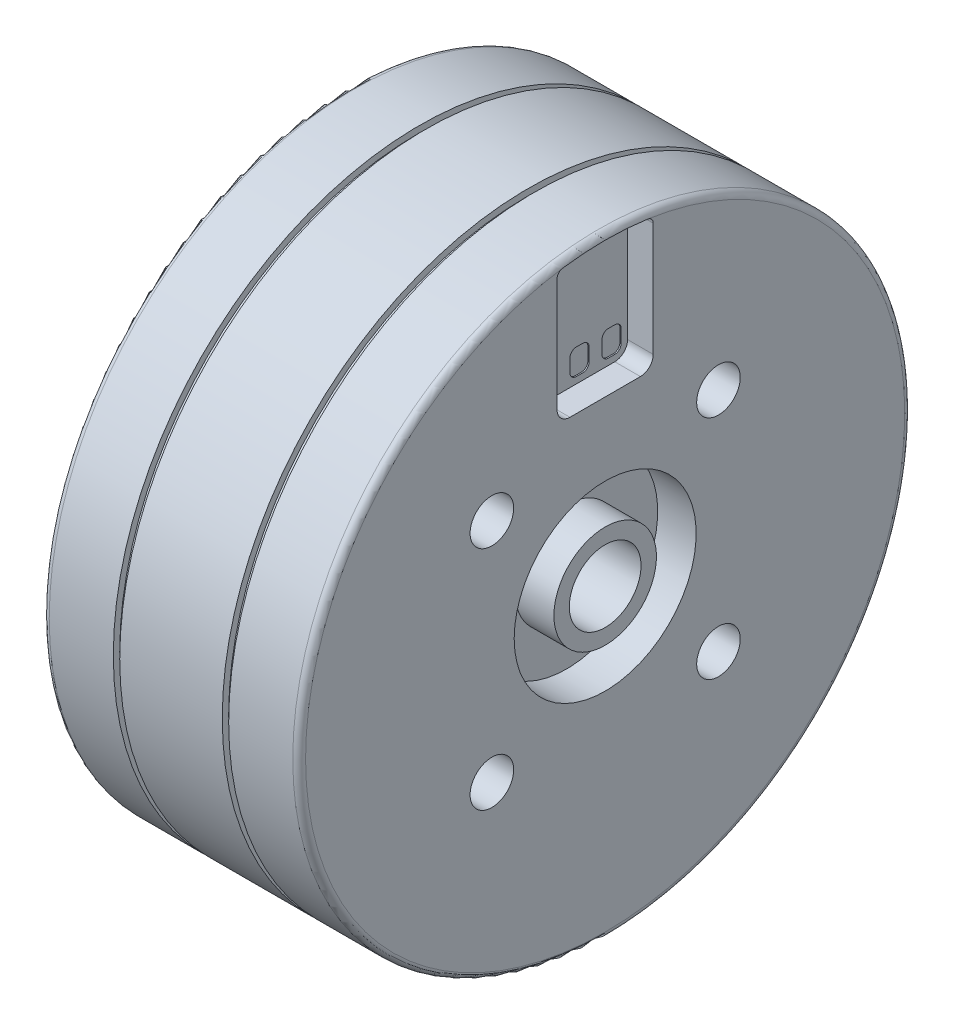
SolidWorks part; units mm, degrees
ref_plane "Plan de face" through (0, 0, 0) normal (0, 0, 1) x (1, 0, 0)
ref_plane "Plan de dessus" through (0, 0, 0) normal (0, 1, 0) x (1, 0, 0)
ref_plane "Plan de droite" through (0, 0, 0) normal (1, 0, 0) x (0, 0, -1)
sketch "Esquisse1" plane through (0, 0, 0) normal (0, 0, 1) x (1, 0, 0)
  line L0 (-88.5968, 0) -> (128.6117, 0) construction
  line L1 (0, 2.8) -> (0, 23.375)
  line L5 (6, 23.875) -> (14, 23.875)
  line L9 (20, 23.375) -> (20, 7.1)
  line L14 (20, 2.8) -> (0, 2.8)
  line L15 (0.5, 23.875) -> (5.5, 23.875)
  line L16 (14.5, 23.875) -> (19.5, 23.875)
  line L17 (5.5, 23.875) -> (5.5, 23.375)
  line L18 (5.5, 23.375) -> (6, 23.375)
  line L19 (6, 23.375) -> (6, 23.875)
  line L20 (14, 23.875) -> (14, 23.375)
  line L21 (14, 23.375) -> (14.5, 23.375)
  line L22 (14.5, 23.375) -> (14.5, 23.875)
  line L24 (17, 7.1) -> (20, 7.1)
  line L25 (20, 2.8) -> (20, 4)
  line L26 (20, 4) -> (17, 4)
  line L27 (17, 4) -> (17, 7.1)
  arc A0 (19.5, 23.875) -> (20, 23.375) centre (19.5, 23.375) cw
  arc A1 (0, 23.375) -> (0.5, 23.875) centre (0.5, 23.375) cw
  dimension "D10" = 0.5
  dimension "D1" = 0.5
  dimension "D2" = 5.6
  dimension "D3" = 14.2
  dimension "D4" = 20
  dimension "D5" = 8
  dimension "D6" = 8
  dimension "D7" = 47.75
  dimension "D8" = 3
revolve "Révolution1" add sketch "Esquisse1" angle 360 about L0
hole_wizard "Dégagement M2.51" positions "Esquisse3" profile "Esquisse4" hole size "M2.5" standard "ISO"
sketch "Esquisse3" plane through (0, 0, 0) normal (-1, 0, 0) x (0, 0, 1)
  point P0 (0, 7.5)
  dimension "D1" = 7.5
sketch "Esquisse4" plane through (0, 7.5, 0) normal (0, 1, 0) x (0, 0, 1)
  line L0 (0, 0) -> (0, 3.3712)
  line L1 (0, 3.3712) -> (1.45, 2.5)
  line L2 (1.45, 2.5) -> (1.45, 0)
  line L5 (1.45, 0) -> (0, 0)
  line L10 (0, 3.3712) -> (-1.45, 2.5) construction
  line L11 (0, -6.35) -> (0, 107.95) construction
  dimension "Diamètre du perçage" = 2.9
  dimension "Profondeur du perçage" = 2.5
  dimension "Angle de pointe" = 118
hole_wizard "Dégagement M31" positions "Esquisse6" profile "Esquisse7" hole size "M3" standard "ISO"
sketch "Esquisse6" plane through (20, 0, 0) normal (1, 0, 0) x (0, 0, -1)
  line L0 (0, -6.6554) -> (0, 7.3657) construction
  line L2 (5.291, -5.291) -> (-5.9943, 5.9943) construction
  point P15 (-8.8388, 8.8388)
  dimension "D1" = 45
  dimension "D2" = 12.5
sketch "Esquisse7" plane through (20, 8.8388, 8.8388) normal (0, 1, 0) x (0, 0, -1)
  line L0 (0, 0) -> (0, 3.5215)
  line L1 (0, 3.5215) -> (1.7, 2.5)
  line L2 (1.7, 2.5) -> (1.7, 0)
  line L5 (1.7, 0) -> (0, 0)
  line L10 (0, 3.5215) -> (-1.7, 2.5) construction
  line L11 (0, -6.35) -> (0, 107.95) construction
  dimension "Diamètre du perçage" = 3.4
  dimension "Profondeur du perçage" = 2.5
  dimension "Angle de pointe" = 118
pattern_circular "Répétition circulaire1" count 4 over 360 about axis through (0, 0, 0) along (1, 0, 0) of "Dégagement M2.51", "Dégagement M31"
sketch "Esquisse9" plane through (20, 0, 0) normal (1, 0, 0) x (0, 0, -1)
  line L0 (2.75, 13.2829) -> (2.25, 13.2829)
  line L1 (0.25, 13.2829) -> (-0.25, 13.2829)
  line L2 (0.75, 13.7829) -> (0.75, 14.7829)
  line L3 (0.25, 15.2829) -> (-0.25, 15.2829)
  line L4 (-0.75, 13.7829) -> (-0.75, 14.7829)
  line L5 (0.75, 13.2829) -> (-0.75, 15.2829) construction
  line L6 (0.75, 15.2829) -> (-0.75, 13.2829) construction
  line L7 (3.25, 13.7829) -> (3.25, 14.7829)
  line L8 (2.75, 15.2829) -> (2.25, 15.2829)
  line L9 (1.75, 13.7829) -> (1.75, 14.7829)
  line L10 (3.25, 13.2829) -> (1.75, 15.2829) construction
  line L11 (3.25, 15.2829) -> (1.75, 13.2829) construction
  line L12 (-2.25, 13.2829) -> (-2.75, 13.2829)
  line L13 (-1.75, 13.7829) -> (-1.75, 14.7829)
  line L14 (-2.25, 15.2829) -> (-2.75, 15.2829)
  line L15 (-3.25, 13.7829) -> (-3.25, 14.7829)
  line L16 (-1.75, 13.2829) -> (-3.25, 15.2829) construction
  line L17 (-1.75, 15.2829) -> (-3.25, 13.2829) construction
  circle A0 centre (0, 0) radius 14.5 construction
  arc A1 (0.75, 14.7829) -> (0.25, 15.2829) centre (0.25, 14.7829) ccw
  arc A2 (-0.25, 15.2829) -> (-0.75, 14.7829) centre (-0.25, 14.7829) ccw
  arc A3 (-0.25, 13.2829) -> (-0.75, 13.7829) centre (-0.25, 13.7829) cw
  arc A4 (0.25, 13.2829) -> (0.75, 13.7829) centre (0.25, 13.7829) ccw
  arc A5 (3.25, 14.7829) -> (2.75, 15.2829) centre (2.75, 14.7829) ccw
  arc A6 (2.25, 15.2829) -> (1.75, 14.7829) centre (2.25, 14.7829) ccw
  arc A7 (2.25, 13.2829) -> (1.75, 13.7829) centre (2.25, 13.7829) cw
  arc A8 (2.75, 13.2829) -> (3.25, 13.7829) centre (2.75, 13.7829) ccw
  arc A9 (-1.75, 14.7829) -> (-2.25, 15.2829) centre (-2.25, 14.7829) ccw
  arc A10 (-2.75, 15.2829) -> (-3.25, 14.7829) centre (-2.75, 14.7829) ccw
  arc A11 (-2.75, 13.2829) -> (-3.25, 13.7829) centre (-2.75, 13.7829) cw
  arc A12 (-2.25, 13.2829) -> (-1.75, 13.7829) centre (-2.25, 13.7829) ccw
  point P3 (0, 14.2829)
  point P21 (2.5, 14.2829)
  point P38 (-2.5, 14.2829)
  dimension "D1" = 29
  dimension "D2" = 0.5
  dimension "D3" = 1.5
  dimension "D4" = 2
  dimension "D7" = 2.5
  dimension "D8" = 2.5
  dimension "D5" = 2
  dimension "D6" = 2
extrude "Enlèv. mat.-Extru.1" cut sketch "Esquisse9" against normal blind 2.1
sketch "Esquisse10" plane through (20, 0, 0) normal (1, 0, 0) x (0, 0, -1)
  line L0 (3.75, 22.6429) -> (3.75, 13.7829)
  line L1 (2.75, 12.7829) -> (-2.75, 12.7829)
  line L2 (-3.75, 13.7829) -> (-3.75, 22.6429)
  line L3 (-2.75, 13.2829) -> (-2.25, 13.2829) construction
  line L4 (-3.25, 14.7829) -> (-3.25, 13.7829) construction
  line L5 (3.25, 13.7829) -> (3.25, 14.7829) construction
  arc A1 (-2.75, 12.7829) -> (-3.75, 13.7829) centre (-2.75, 13.7829) cw
  arc A2 (3.75, 13.7829) -> (2.75, 12.7829) centre (2.75, 13.7829) cw
  circle A5 centre (0, 0) radius 23.375 construction
  arc A6 (3.321, 23.1379) -> (-3.321, 23.1379) centre (0, 0) ccw
  arc A7 (-3.75, 22.6429) -> (-3.321, 23.1379) centre (-3.25, 22.6429) cw
  arc A8 (3.75, 22.6429) -> (3.321, 23.1379) centre (3.25, 22.6429) ccw
  dimension "D4" = 1
  dimension "D5" = 0.5
  dimension "D1" = 0.5
  dimension "D2" = 0.5
  dimension "D3" = 0.5
extrude "Enlèv. mat.-Extru.2" cut sketch "Esquisse10" against normal blind 2
